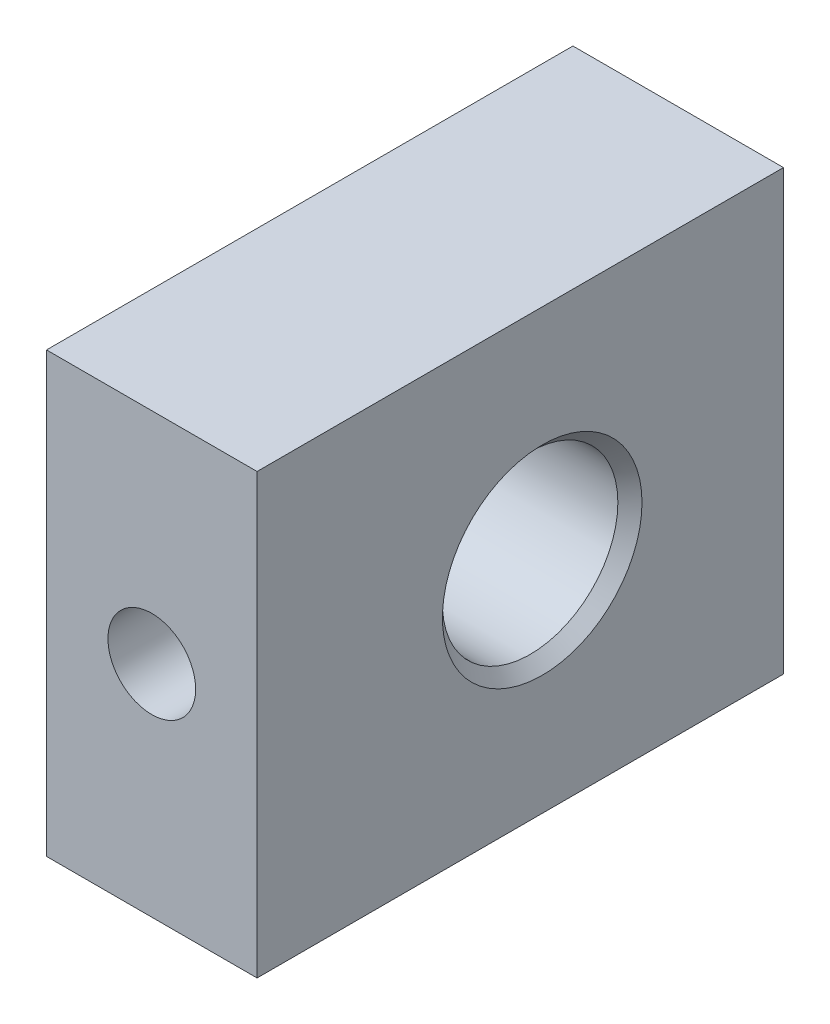
SolidWorks part; units mm, degrees
ref_plane "Front" through (0, 0, 0) normal (0, 0, 1) x (1, 0, 0)
ref_plane "Top" through (0, 0, 0) normal (0, 1, 0) x (1, 0, 0)
ref_plane "Right" through (0, 0, 0) normal (1, 0, 0) x (0, 0, -1)
sketch "Эскиз1" plane through (0, 0, 0) normal (0, 0, 1) x (1, 0, 0)
  line L1 (-2.4, -5) -> (2.4, -5)
  line L2 (-2.4, -5) -> (-2.4, 5)
  line L3 (-2.4, 5) -> (2.4, 5)
  line L4 (2.4, -5) -> (2.4, 5)
  line L5 (-2.4, -5) -> (2.4, 5) construction
  line L6 (-2.4, 5) -> (2.4, -5) construction
  point P0 (0, 0)
  dimension "D1" = 10
  dimension "D2" = 4.8
extrude "Бобышка-Вытянуть1" add sketch "Эскиз1" along normal blind 12
hole_wizard "Отверстие обработанное метчиком M41" positions "Эскиз3" profile "Эскиз2" tap size "M4" standard "DIN" end condition through all
sketch "Эскиз3" plane through (2.4, 0, 0) normal (1, 0, 0) x (0, 0, -1)
  line L3 (0, -5) -> (0, 5) construction
  line L4 (-12, -5) -> (0, -5) construction
  point P0 (-5.5, 0)
  dimension "D1" = 5.5
  dimension "D2" = 5
sketch "Эскиз2" plane through (2.4, 0, 5.5) normal (0, 1, 0) x (0, 0, -1)
  line L0 (0, 0) -> (0, 4.8)
  line L1 (0, 4.8) -> (2.275, 4.8)
  line L2 (2, 4.525) -> (2, 0.275)
  line L3 (2, 0.275) -> (2.275, 0)
  line L5 (2.275, 0) -> (0, 0)
  line L6 (-2, 0.275) -> (-2.275, 0) construction
  line L7 (2.275, 4.8) -> (2, 4.525)
  line L8 (-2.275, 4.8) -> (-2, 4.525) construction
  line L11 (0, -6.35) -> (0, 107.95) construction
  dimension "Диаметр резьбы" = 4
  dimension "Глубина проходного сверла" = 4.8
  dimension "Диаметр передней зенковки" = 4.55
  dimension "Угол передней зенковки" = 90
  dimension "Диаметр задней зенковки" = 4.55
  dimension "Угол задней зенковки" = 90
sketch "Эскиз4" plane through (0, 0, 12) normal (0, 0, 1) x (1, 0, 0)
  circle A0 centre (0, 0) radius 1
  dimension "D1" = 2
extrude "Вырез-Вытянуть1" cut sketch "Эскиз4" against normal up to next
